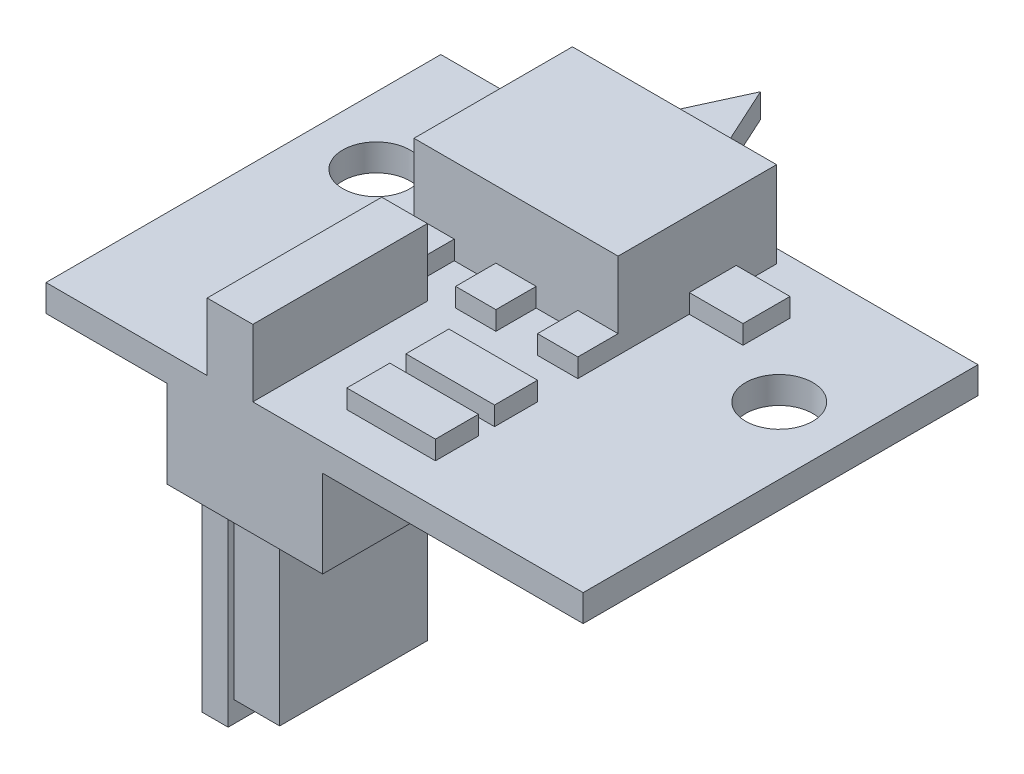
SolidWorks part; units mm, degrees
ref_plane "前视基准面" through (0, 0, 0) normal (0, 0, 1) x (1, 0, 0)
ref_plane "上视基准面" through (0, 0, 0) normal (0, 1, 0) x (1, 0, 0)
ref_plane "右视基准面" through (0, 0, 0) normal (1, 0, 0) x (0, 0, -1)
sketch "草图1" plane through (0, 0, 0) normal (0, 1, 0) x (1, 0, 0)
  line L0 (-198.4701, 0) -> (238.3503, 0) construction
  line L1 (0, 180.7887) -> (0, -203.8222) construction
  line L2 (-10, 4.9) -> (-10, -9.8)
  line L3 (-10, -9.8) -> (10, -9.8)
  line L4 (10, -9.8) -> (10, 4.9)
  line L5 (10, 4.9) -> (-10, 4.9)
  circle A0 centre (-7.5, 0) radius 1.25
  circle A1 centre (7.5, 0) radius 1.25
  point P13 (0, 0)
  dimension "D3" = 2.5
  dimension "D1" = 20
  dimension "D2" = 14.7
  dimension "D4" = 15
  dimension "D5" = 4.9
extrude "凸台-拉伸1" add sketch "草图1" along normal blind 1
sketch "草图2" plane through (0, 1, 0) normal (0, 1, 0) x (1, 0, 0)
  line L0 (-4.6, 4.4) -> (3, 4.4)
  line L1 (3, 4.4) -> (3, -1.5)
  line L2 (3, -1.5) -> (-4.6, -1.5)
  line L3 (-4.6, -1.5) -> (-4.6, 4.4)
  line L4 (10, 4.9) -> (-10, 4.9) construction
  line L5 (10, -9.8) -> (10, 4.9) construction
  point P2 (0, 0)
  dimension "D1" = 0.5
  dimension "D2" = 7.6
  dimension "D3" = 5.9
  dimension "D4" = 7
extrude "凸台-拉伸2" add sketch "草图2" along normal blind 3.2
sketch "草图3" plane through (0, 0, -4.4) normal (0, 0, -1) x (-1, 0, 0)
  line L0 (0.8, -2.3547) -> (0.8, 7.4536) construction
  line L1 (7.641, 2.6) -> (-8.5598, 2.6) construction
  line L2 (-3, 4.2) -> (-3, 1) construction
  line L3 (4.6, 4.2) -> (4.6, 1) construction
  line L4 (-3, 4.2) -> (4.6, 4.2) construction
  line L5 (-3, 1) -> (4.6, 1) construction
  line L6 (2.265, 2.15) -> (2.265, 3.05)
  line L7 (2.265, 3.05) -> (-0.665, 3.05)
  line L8 (-0.665, 3.05) -> (-0.665, 2.15)
  line L9 (-0.665, 2.15) -> (2.265, 2.15)
  point P14 (0, 0)
  dimension "D1" = 2.93
  dimension "D2" = 0.9
extrude "凸台-拉伸3" add sketch "草图3" along normal blind 3.2
sketch "草图4" plane through (0, 3.05, 0) normal (0, 1, 0) x (1, 0, 0)
  line L0 (-0.8, 7.6) -> (-2.265, 4.4)
  line L1 (-2.265, 7.6) -> (0.665, 7.6) construction
  line L2 (-2.265, 4.4) -> (0.665, 4.4) construction
  line L3 (-2.265, 4.4) -> (-2.265, 7.6)
  line L4 (-2.265, 7.6) -> (-0.8, 7.6) construction
  line L5 (-0.8, 7.6) -> (0.665, 7.6) construction
  line L6 (0.665, 7.6) -> (0.665, 4.4)
  line L7 (0.665, 4.4) -> (-0.8, 7.6)
  line L8 (-2.265, 7.6) -> (-2.265, 7.985)
  line L9 (-2.265, 7.985) -> (0.665, 7.985)
  line L10 (0.665, 7.985) -> (0.665, 7.6)
extrude "切除-拉伸1" cut sketch "草图4" against normal up to next
sketch "草图5" plane through (0, 1, 0) normal (0, 1, 0) x (1, 0, 0)
  line L0 (3, 2.9) -> (5, 2.9)
  line L1 (3, -1.5) -> (3, 4.4) construction
  line L2 (5, 2.9) -> (5, 1.15)
  line L3 (5, 1.15) -> (3, 1.15)
  line L4 (3, 1.15) -> (3, 2.9)
  line L5 (-4.6, 2.9) -> (-6.6, 2.9)
  line L6 (-4.6, 4.4) -> (-4.6, -1.5) construction
  line L7 (-6.6, 2.9) -> (-6.6, 1.15)
  line L8 (-6.6, 1.15) -> (-4.6, 1.15)
  line L9 (-4.6, 1.15) -> (-4.6, 2.9)
  line L10 (-4.6, -1.5) -> (-4.6, -3)
  line L11 (-4.6, -1.5) -> (3, -1.5) construction
  line L12 (-4.6, -3) -> (-3.1, -3)
  line L13 (-3.1, -3) -> (-3.1, -1.5)
  line L14 (-3.1, -1.5) -> (-4.6, -1.5)
  line L15 (-1.55, -1.5) -> (-1.55, -3)
  line L16 (-1.55, -3) -> (-0.05, -3)
  line L17 (-0.05, -3) -> (-0.05, -1.5)
  line L18 (-0.05, -1.5) -> (-1.55, -1.5)
  line L19 (1.5, -1.5) -> (1.5, -3)
  line L20 (1.5, -3) -> (3, -3)
  line L21 (3, -3) -> (3, -1.5)
  line L22 (3, -1.5) -> (1.5, -1.5)
  line L23 (-0.3, -4.5) -> (3, -4.5)
  line L24 (3, -4.5) -> (3, -6.1)
  line L25 (3, -6.1) -> (-0.3, -6.1)
  line L27 (-0.3, -4.5) -> (-0.3, -6.1)
  line L28 (-0.3, -6.7) -> (3, -6.7)
  line L29 (3, -6.7) -> (3, -8.3)
  line L30 (3, -8.3) -> (-0.3, -8.3)
  line L31 (-0.3, -8.3) -> (-0.3, -6.7)
  line L32 (10, 4.9) -> (-10, 4.9) construction
  line L33 (10, -9.8) -> (10, 4.9) construction
  line L34 (-10, -9.8) -> (10, -9.8) construction
  point P25 (0, 0)
  point P29 (0, 0)
  dimension "D1" = 1.75
  dimension "D2" = 2
  dimension "D3" = 2
  dimension "D4" = 1.5
  dimension "D5" = 1.55
  dimension "D6" = 1.5
  dimension "D7" = 3.3
  dimension "D8" = 1.6
  dimension "D9" = 7
  dimension "D10" = 1.5
  dimension "D11" = 1.5
extrude "凸台-拉伸4" add sketch "草图5" along normal blind 0.7
sketch "草图6" plane through (0, 1, 0) normal (0, 1, 0) x (1, 0, 0)
  line L0 (-4, -3.3) -> (-2.3, -3.3)
  line L1 (-2.3, -3.3) -> (-2.3, -9.8)
  line L2 (-10, -9.8) -> (10, -9.8) construction
  line L3 (-2.3, -9.8) -> (-4, -9.8)
  line L4 (-4, -9.8) -> (-4, -3.3)
  line L5 (-10, 4.9) -> (-10, -9.8) construction
  dimension "D1" = 6
  dimension "D2" = 1.7
  dimension "D3" = 6.5
extrude "凸台-拉伸5" add sketch "草图6" along normal blind 2.5
sketch "草图7" plane through (0, 0, 0) normal (0, -1, 0) x (1, 0, 0)
  line L0 (0.3, 9.8) -> (-5.5, 9.8)
  line L1 (-10, 9.8) -> (10, 9.8) construction
  line L2 (-5.5, 9.8) -> (-5.5, 2.2)
  line L3 (-5.5, 2.2) -> (0.3, 2.2)
  line L4 (0.3, 2.2) -> (0.3, 9.8)
  line L5 (-10, -4.9) -> (-10, 9.8) construction
  dimension "D1" = 5.8
  dimension "D2" = 7.6
  dimension "D3" = 4.5
extrude "凸台-拉伸6" add sketch "草图7" along normal blind 3.25
sketch "草图8" plane through (0, -3.25, 0) normal (0, -1, 0) x (1, 0, 0)
  line L0 (-5.5, 3.5) -> (-5.5, 8.5)
  line L1 (-5.5, 9.8) -> (-5.5, 2.2) construction
  line L2 (-5.5, 8.5) -> (-4.52, 8.5)
  line L3 (-4.52, 8.5) -> (-4.52, 3.5)
  line L4 (-4.52, 3.5) -> (-5.5, 3.5)
  line L5 (-5.5, 2.2) -> (0.3, 2.2) construction
  dimension "D1" = 5
  dimension "D2" = 1.3
  dimension "D3" = 0.98
extrude "凸台-拉伸7" add sketch "草图8" along normal blind 8
sketch "草图9" plane through (0, -3.25, 0) normal (0, -1, 0) x (1, 0, 0)
  line L0 (-4, 3.3) -> (-2.3, 3.3) construction
  line L1 (-4, 9.8) -> (-4, 3.3) construction
  line L3 (-2.3, 3.3) -> (-2.3, 9.8) construction
  line L4 (-4, 3.3) -> (-2.3, 3.3)
  line L5 (-4, 8.8) -> (-4, 3.3)
  line L6 (-2.3, 8.8) -> (-4, 8.8)
  line L7 (-2.3, 3.3) -> (-2.3, 8.8)
  line L9 (0.3, 9.8) -> (-5.5, 9.8) construction
  dimension "D1" = 1
extrude "凸台-拉伸8" add sketch "草图9" along normal blind 6.7
